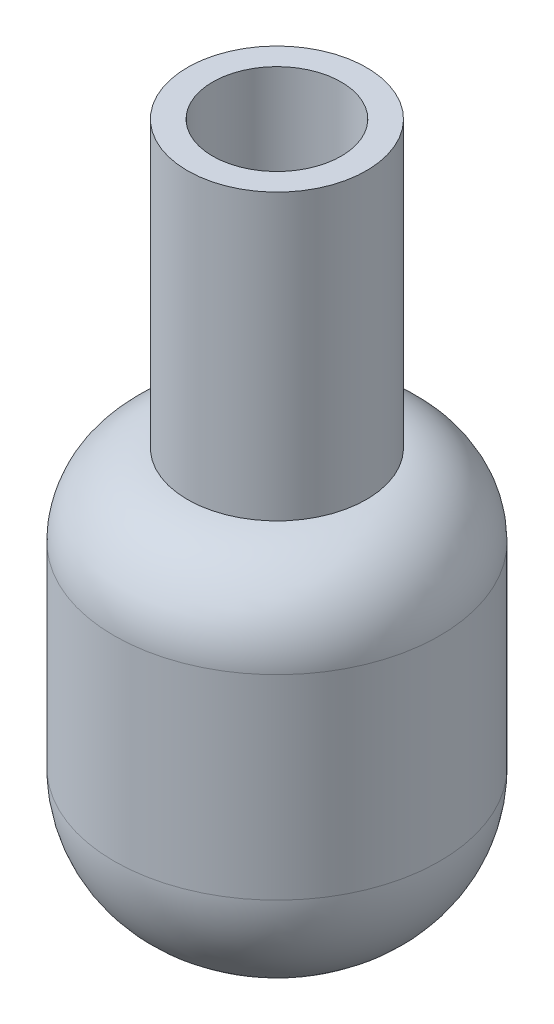
SolidWorks part; units mm, degrees
ref_plane "Front Plane" through (0, 0, 0) normal (0, 0, 1) x (1, 0, 0)
ref_plane "Top Plane" through (0, 0, 0) normal (0, 1, 0) x (1, 0, 0)
ref_plane "Right Plane" through (0, 0, 0) normal (1, 0, 0) x (0, 0, -1)
sketch "Sketch1" plane through (0, 0, 0) normal (0, 1, 0) x (1, 0, 0)
  circle A0 centre (0, 0) radius 25.4
  dimension "D1" = 50.8
extrude "Boss-Extrude1" add sketch "Sketch1" along normal blind 63.5
fillet "Fillet2" radius 20.32 1 edges at (0, 0, 25.4)
fillet "Fillet3" radius 12.7 1 edges at (0, 63.5, 25.4)
sketch "Sketch2" plane through (0, 63.5, 0) normal (0, 1, 0) x (1, 0, 0)
  circle A1 centre (0, 0) radius 13.97
  dimension "D1" = 27.94
extrude "Boss-Extrude2" add sketch "Sketch2" along normal blind 44.45
sketch "Sketch4" plane through (0, 107.95, 0) normal (0, 1, 0) x (1, 0, 0)
  circle A0 centre (0, 0) radius 10.033
  dimension "D1" = 20.066
extrude "Cut-Extrude1" cut sketch "Sketch4" against normal blind 50.8
sketch "Sketch11" plane through (0, 0, 0) normal (0, 0, 1) x (1, 0, 0)
  line L0 (13.97, 107.95) -> (-13.97, 107.95) construction
  circle A0 centre (0, 88.9) radius 5
  dimension "D2" = 10
  dimension "D1" = 19.05
extrude "Cut-Extrude2" cut sketch "Sketch11" against normal up to next
